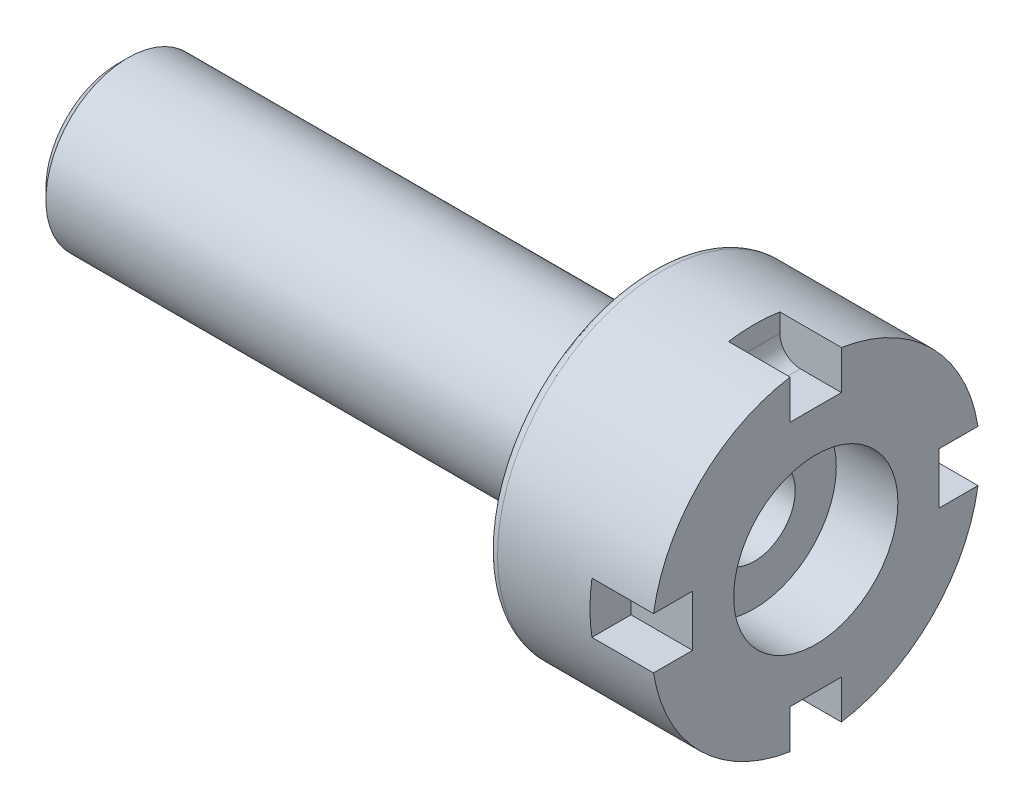
SolidWorks part; units mm, degrees
ref_plane "Płaszczyzna przednia" through (0, 0, 0) normal (0, 0, 1) x (1, 0, 0)
ref_plane "Płaszczyzna górna" through (0, 0, 0) normal (0, 1, 0) x (1, 0, 0)
ref_plane "Płaszczyzna prawa" through (0, 0, 0) normal (1, 0, 0) x (0, 0, -1)
ref_axis "Oś1" through (-88.99, 0, 0) along (1, 0, 0)
sketch "Szkic2" plane through (0, 0, 0) normal (0, 0, 1) x (1, 0, 0)
  line L0 (-293.4857, 20) -> (46.5143, 20)
  line L1 (46.5143, 80) -> (-33.4857, 80)
  line L2 (-33.4857, 80) -> (-33.4857, 40)
  line L3 (-33.4857, 40) -> (-293.4857, 40)
  line L4 (-293.4857, 40) -> (-293.4857, 20)
  line L5 (46.5143, 80) -> (46.5143, 20)
  line L6 (-88.99, 0) -> (88.99, 0) construction
  point P8 (-278.8921, 12.4349)
  dimension "D1" = 40
  dimension "D2" = 80
  dimension "D3" = 340
  dimension "D4" = 160
  dimension "D5" = 80
revolve "Obrót1" add sketch "Szkic2" angle 360 about axis through (-88.99, 0, 0) along (1, 0, 0)
sketch "Szkic3" plane through (46.5143, 0, 0) normal (1, 0, 0) x (0, 0, -1)
  line L1 (-12.5, 90) -> (12.5, 90)
  line L2 (-12.5, 90) -> (-12.5, 60)
  line L3 (-12.5, 60) -> (12.5, 60)
  line L4 (12.5, 90) -> (12.5, 60)
  line L5 (-12.5, 90) -> (12.5, 60) construction
  line L6 (-12.5, 60) -> (12.5, 90) construction
  circle A0 centre (0, 0) radius 40
  point P4 (432.8174, 275.5801)
  point P6 (0, 75)
  dimension "D1" = 80
  dimension "D2" = 25
  dimension "D3" = 30
  dimension "D4" = 60
extrude "Wytnij-wyciągnięcie1" cut sketch "Szkic3" against normal blind 30
fillet "Zaokrąglenie1" radius 10 1 edges at (16.5143, 60, 0)
pattern_circular "Szyk kołowy1" count 4 over 360 about axis through (0, 0, 0) along (1, 0, 0) of "Wytnij-wyciągnięcie1"
fillet "Zaokrąglenie2" radius 5 2 edges at (-33.4857, 0, 80) (-33.4857, 0, 40)
chamfer "Sfazowanie2" distance 5 angle 45 2 edges at (-293.4857, 0, 40) (-293.4857, 0, 20)
